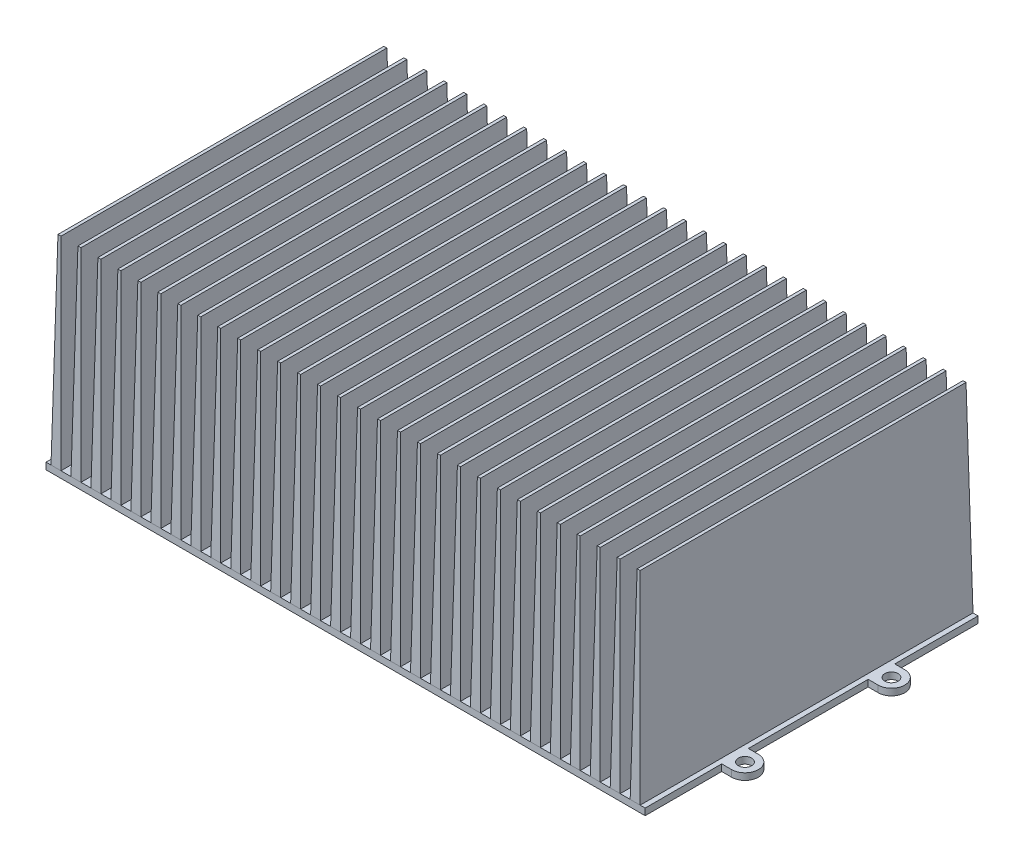
SolidWorks part; units mm, degrees
ref_plane "Front Plane" through (0, 0, 0) normal (0, 0, 1) x (1, 0, 0)
ref_plane "Top Plane" through (0, 0, 0) normal (0, 1, 0) x (1, 0, 0)
ref_plane "Right Plane" through (0, 0, 0) normal (1, 0, 0) x (0, 0, -1)
sketch "Sketch1" plane through (0, 0, 0) normal (0, 1, 0) x (1, 0, 0)
  line L1 (90, -50) -> (-90, -50)
  line L2 (90, -50) -> (90, 50)
  line L3 (90, 50) -> (-90, 50)
  line L4 (-90, -50) -> (-90, 50)
  line L5 (90, -50) -> (-90, 50) construction
  line L6 (90, 50) -> (-90, -50) construction
  point P0 (0, 0)
  dimension "D1" = 100
  dimension "D2" = 180
extrude "Boss-Extrude1" add sketch "Sketch1" along normal blind 2
sketch "Sketch2" plane through (0, 2, 0) normal (0, 1, 0) x (1, 0, 0)
  line L5 (-90, -50) -> (90, -50) construction
  line L6 (88.5, -50) -> (85.5, -50)
  line L7 (88.5, -50) -> (88.5, 50)
  line L8 (88.5, 50) -> (85.5, 50)
  line L9 (85.5, -50) -> (85.5, 50)
  line L10 (90, 50) -> (-90, 50) construction
  line L11 (90, 0) -> (88.5, 0) construction
  line L12 (90, -50) -> (90, 50) construction
  dimension "D1" = 1.5
  dimension "D2" = 3
extrude "Boss-Extrude2" add sketch "Sketch2" along normal blind 60 draft 1
pattern_linear "LPattern1" count 30 spacing 6 along (-1, 0, 0) of "Boss-Extrude2"
sketch "Sketch3" plane through (0, 2, 0) normal (0, 1, 0) x (1, 0, 0)
  line L0 (90, -50) -> (90, -23) construction
  line L1 (90, -50) -> (90, 50) construction
  line L2 (90, -23) -> (93, -23) construction
  line L3 (93, -19) -> (90, -19)
  line L4 (93, -27) -> (90, -27)
  circle A0 centre (93, -23) radius 2
  arc A1 (93, -27) -> (93, -19) centre (93, -23) ccw
  line M5 (90, -50) -> (90, 50)
  dimension "D2" = 3
  dimension "D3" = 4
  dimension "D4" = 4
  dimension "D1" = 27
extrude "Boss-Extrude3" add sketch "Sketch3" against normal blind 2 contours L4 A1 L3 A0 M5
pattern_linear "LPattern2" count 2 spacing 44 along (0, 0, -1) of "Boss-Extrude3"
mirror "Mirror2" about plane through (0, 0, 0) normal (1, 0, 0) of "LPattern2", "Boss-Extrude3"
equation "\"width\"= \"D2@Sketch1\""
equation "\"D1@Sketch1\"= \"width\" / 2 + 10"
equation "\"D1@Boss-Extrude2\"= \"width\" / 3"
equation "\"D1@LPattern1\" = \"width\" / 6"
equation "\"numFins\"= \"D1@LPattern1\""
equation "\"D1@Sketch2\"= ( \"width\" - 3 * ( 2 * \"numFins\" - 1 ) ) / 2"
equation "\"D1@Sketch3\"= ( \"D1@Sketch1\" - 46 ) / 2"
